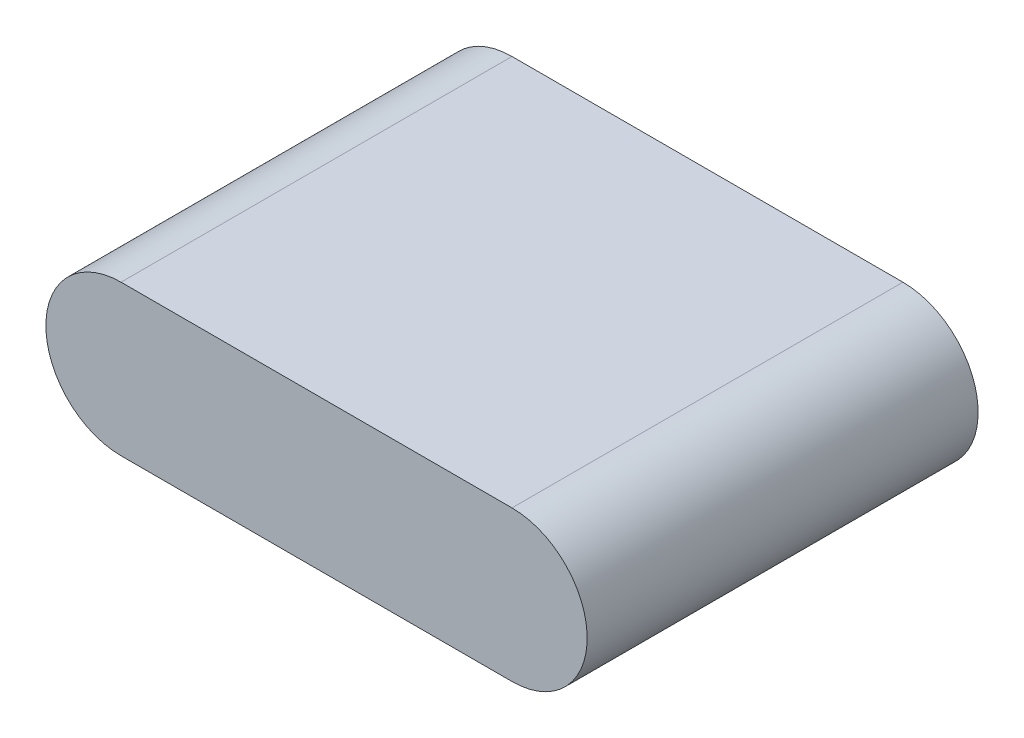
SolidWorks part; units mm, degrees
ref_plane "Plan de face" through (0, 0, 0) normal (0, 0, 1) x (1, 0, 0)
ref_plane "Plan de dessus" through (0, 0, 0) normal (0, 1, 0) x (1, 0, 0)
ref_plane "Plan de droite" through (0, 0, 0) normal (1, 0, 0) x (0, 0, -1)
sketch "Esquisse1" plane through (0, 0, 0) normal (0, 0, 1) x (1, 0, 0)
  line L0 (0, 0) -> (78, 0) construction
  line L1 (0, 15) -> (78, 15)
  line L2 (0, -15) -> (78, -15)
  line L3 (-15, 0) -> (0, 0) construction
  line L4 (78, 0) -> (93, 0) construction
  arc A0 (0, 15) -> (0, -15) centre (0, 0) ccw
  arc A1 (78, -15) -> (78, 15) centre (78, 0) ccw
  point P3 (39, 0)
  dimension "D1" = 30
  dimension "D2" = 108
extrude "Boss.-Extru.1" add sketch "Esquisse1" along normal blind 78
sketch "Esquisse2" plane through (0, 0, 0) normal (0, 0, -1) x (-1, 0, 0)
  line L0 (-39, 15) -> (-39, -15) construction
  line L1 (-78, 15) -> (0, 15) construction
  line L2 (0, -15) -> (-78, -15) construction
ref_plane "Plan1" through (39, 0, 0) normal (1, 0, 0) x (0, -1, 0)
